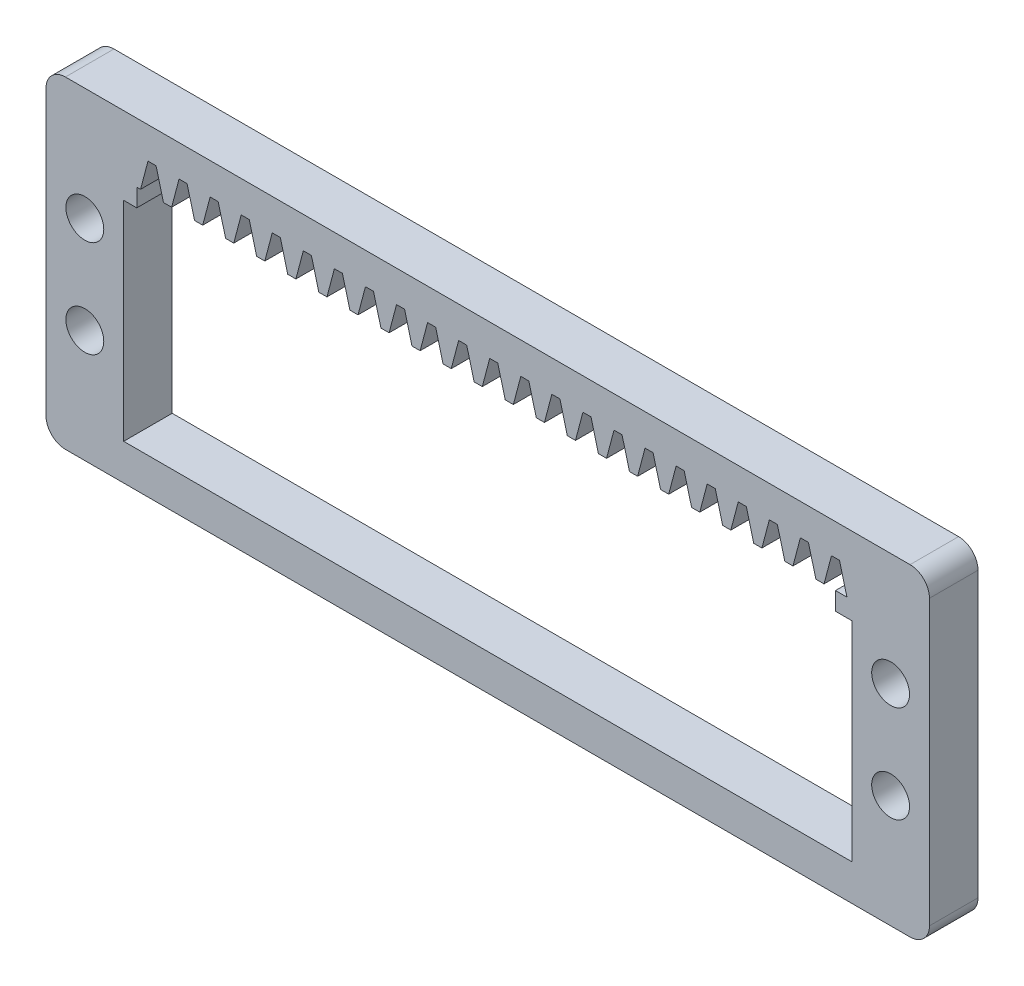
SolidWorks part; units mm, degrees
other "Markup1"
sketch "Sketch6" plane through (0, -30, 3.6) normal (0, 0, 1) x (1, 0, 0)
other "Markup2"
sketch "Sketch7" plane through (0, -30, 3.6) normal (0, 0, 1) x (1, 0, 0)
ref_plane "Front Plane" through (0, 0, 0) normal (0, 0, 1) x (1, 0, 0)
ref_plane "Top Plane" through (0, 0, 0) normal (0, 1, 0) x (1, 0, 0)
ref_plane "Right Plane" through (0, 0, 0) normal (1, 0, 0) x (0, 0, -1)
sketch "Sketch1" plane through (0, 0, 0) normal (0, 0, 1) x (1, 0, 0)
  line L1 (2, 0) -> (89, 0)
  line L2 (0, -2) -> (0, -31.22)
  line L3 (2, -33.22) -> (89, -33.22)
  line L4 (91, -2) -> (91, -31.22)
  arc A0 (89, -33.22) -> (91, -31.22) centre (89, -31.22) ccw
  arc A1 (0, -31.22) -> (2, -33.22) centre (2, -31.22) ccw
  arc A2 (2, 0) -> (0, -2) centre (2, -2) ccw
  arc A3 (89, 0) -> (91, -2) centre (89, -2) cw
  point P7 (91, -33.22)
  point P12 (0, 0)
  point P15 (91, 0)
  dimension "D3" = 2
  dimension "D1" = 33.22
  dimension "D2" = 91
extrude "Boss-Extrude1" add sketch "Sketch1" along normal blind 5
sketch "Sketch2" plane through (0, 0, 5) normal (0, 0, 1) x (1, 0, 0)
  line L0 (2, -33.22) -> (89, -33.22) construction
  line L1 (8, -8) -> (83, -8)
  line L2 (8, -8) -> (8, -29.5)
  line L3 (8, -29.5) -> (83, -29.5)
  line L4 (83, -8) -> (83, -29.5)
  line L5 (0, -2) -> (0, -31.22) construction
  line L7 (91, -31.22) -> (91, -2) construction
  line L8 (8, -18.75) -> (83, -18.75) construction
  line L12 (8, -29.5) -> (83, -29.5) construction
  line L13 (83, -4.3144) -> (83, -29.5) construction
  dimension "D1" = 21.5
  dimension "D2" = 8
  dimension "D3" = 8
  dimension "D4" = 3.72
extrude "Cut-Extrude1" cut sketch "Sketch2" against normal through all
sketch "Sketch3" plane through (0, 0, 5) normal (0, 0, 1) x (1, 0, 0)
  line L0 (83, -8) -> (8, -8) construction
  line L1 (9.35, -8) -> (81.32, -8)
  line L2 (9.35, -8) -> (9.35, -6.15)
  line L3 (9.35, -6.15) -> (81.32, -6.15)
  line L4 (81.32, -8) -> (81.32, -6.15)
  line L5 (83, -29.5) -> (83, -8) construction
  line L6 (8, -8) -> (8, -29.5) construction
  dimension "D1" = 1.85
  dimension "D2" = 1.68
  dimension "D3" = 1.35
extrude "Cut-Extrude2" cut sketch "Sketch3" against normal through all
sketch "Sketch4" plane through (0, 0, 5) normal (0, 0, 1) x (1, 0, 0)
  line L0 (83.7, -6.15) -> (82.5, -6.15) construction
  line L1 (81.32, -6.15) -> (9.35, -6.15) construction
  line L2 (83.7, -6.15) -> (84.465, -3.2492) construction
  line L3 (84.465, -3.2492) -> (81.735, -3.2492) construction
  line L4 (81.735, -3.2492) -> (82.5, -6.15)
  line L5 (81.735, -3.2492) -> (80.905, -3.2492)
  line L6 (80.905, -3.2492) -> (80.14, -6.15)
  line L7 (80.14, -6.15) -> (82.5, -6.15)
  line L10 (82.5, -6.15) -> (83.7, -6.15) construction
  dimension "D1" = 1.2
  dimension "D3" = 3
  dimension "D4" = 0.83
  dimension "D5" = 2.73
extrude "Cut-Extrude4" cut sketch "Sketch4" against normal through all
pattern_linear "LPattern1" count 23 spacing 3.2 along (-1, 0, 0) of "Cut-Extrude4"
sketch "Sketch5" plane through (0, 0, 5) normal (0, 0, 1) x (1, 0, 0)
  line L0 (83, -16.61) -> (91, -16.61) construction
  line L1 (89, 0) -> (2, 0) construction
  line L2 (8, -8) -> (8, -29.5) construction
  line L3 (0, -2) -> (0, -31.22) construction
  line L4 (2, -33.22) -> (89, -33.22) construction
  line L5 (0, -16.61) -> (8, -16.61) construction
  line L7 (87, -11.61) -> (87, -21.61) construction
  line L8 (4, -11.61) -> (4, -21.61) construction
  line L9 (83, -29.5) -> (83, -8) construction
  line L10 (91, -31.22) -> (91, -2) construction
  circle A4 centre (4, -11.61) radius 1.95
  circle A5 centre (4, -21.61) radius 1.95
  circle A6 centre (87, -11.61) radius 1.95
  circle A7 centre (87, -21.61) radius 1.95
  point P8 (87, -16.61)
  point P18 (4, -16.61)
  point P22 (4, -16.61)
  point P31 (87, -16.61)
  dimension "D1" = 3.9
  dimension "D3" = 3.9
  dimension "D4" = 3.9
  dimension "D6" = 3.9
  dimension "D5" = 10
  dimension "D7" = 10
extrude "Cut-Extrude5" cut sketch "Sketch5" against normal blind 10
